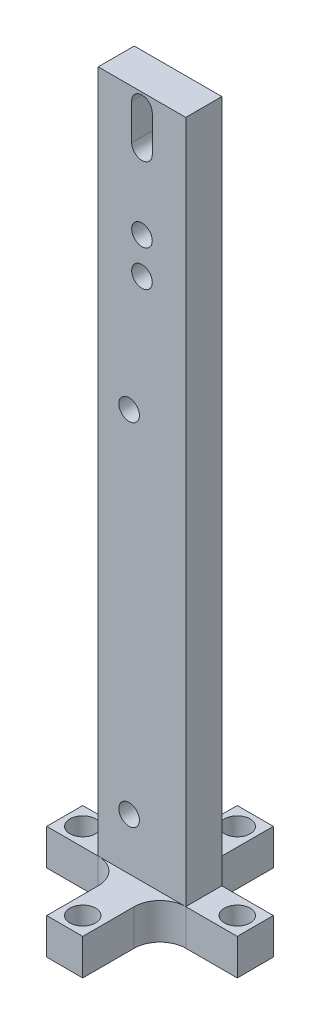
SolidWorks part; units mm, degrees
ref_plane "Front Plane" through (0, 0, 0) normal (0, 0, 1) x (1, 0, 0)
ref_plane "Top Plane" through (0, 0, 0) normal (0, 1, 0) x (1, 0, 0)
ref_plane "Right Plane" through (0, 0, 0) normal (1, 0, 0) x (0, 0, -1)
sketch "Sketch1" plane through (0, 0, 0) normal (0, 1, 0) x (1, 0, 0)
  line L1 (8.5, -3.5) -> (-8.5, -3.5)
  line L2 (8.5, -3.5) -> (8.5, 3.5)
  line L3 (8.5, 3.5) -> (-8.5, 3.5)
  line L4 (-8.5, -3.5) -> (-8.5, 3.5)
  line L5 (8.5, -3.5) -> (-8.5, 3.5) construction
  line L6 (8.5, 3.5) -> (-8.5, -3.5) construction
  point P0 (0, 0)
  dimension "D1" = 7
  dimension "D2" = 17
extrude "Boss-Extrude1" add sketch "Sketch1" along normal blind 139.7
sketch "Sketch2" plane through (0, 0, 0) normal (0, 1, 0) x (1, 0, 0)
  line L0 (-3.5, 3.5) -> (-3.5, 18.5)
  line L1 (-3.5, 18.5) -> (3.5, 18.5)
  line L2 (3.5, 18.5) -> (3.5, 3.5)
  line L3 (-3.5, 3.5) -> (-8.5, 3.5)
  line L4 (-8.5, 3.5) -> (-8.5, -3.5)
  line L5 (-8.5, -3.5) -> (8.5, -3.5)
  line L6 (8.5, -3.5) -> (8.5, 3.5)
  line L7 (8.5, 3.5) -> (-8.5, 3.5)
  line L9 (-8.5, -3.5) -> (-3.5, -3.5)
  line L11 (8.5, 3.5) -> (3.5, 3.5)
  line L12 (8.5, 3.5) -> (-8.5, 3.5) construction
  line L13 (-1000, 0) -> (49000, 0) construction
  line L14 (0, -1000) -> (0, 0) construction
  line L15 (3.5, -18.5) -> (3.5, -3.5)
  line L16 (-3.5, -18.5) -> (3.5, -18.5)
  line L17 (-3.5, -3.5) -> (-3.5, -18.5)
  line L18 (3.5, -3.5) -> (8.5, -3.5)
  line L19 (0, 3.5) -> (0, 49000) construction
  line L20 (8.5, 3.5) -> (18.5, 3.5)
  line L21 (18.5, 3.5) -> (18.5, -3.5)
  line L22 (18.5, -3.5) -> (8.5, -3.5)
  line L23 (8.5, 3.5) -> (8.5, -3.5) construction
  line L24 (-8.5, 3.5) -> (-18.5, 3.5)
  line L25 (-18.5, 3.5) -> (-18.5, -3.5)
  line L26 (-18.5, -3.5) -> (-8.5, -3.5)
  circle A0 centre (0, 15) radius 2.5
  circle A1 centre (15, 0) radius 2.5
  circle A2 centre (0, -15) radius 2.5
  circle A3 centre (-15, 0) radius 2.5
  point P8 (0, 18.5)
  point P37 (0, 0)
  dimension "D6" = 5
  dimension "D2" = 15
  dimension "D3" = 7
  dimension "D4" = 10
  dimension "D5" = 15
  dimension "D1" = 0
  dimension "D7" = 4
extrude "Boss-Extrude2" add sketch "Sketch2" along normal blind 7
fillet "Fillet1" radius 5 4 edges at (-3.5, 3.5, -3.5) (3.5, 3.5, -3.5) (3.5, 3.5, 3.5) (-3.5, 3.5, 3.5)
sketch "Sketch3" plane through (0, 0, 3.5) normal (0, 0, 1) x (1, 0, 0)
  line L0 (-2.5, 85.072) -> (-2.5, 17) construction
  line L1 (-8.5, 7) -> (8.5, 7) construction
  line L2 (-8.5, 139.7) -> (-8.5, 7) construction
  circle A0 centre (-2.5, 85.072) radius 2
  circle A1 centre (-2.5, 17) radius 2
  dimension "D1" = 4
  dimension "D2" = 68.072
  dimension "D3" = 10
  dimension "D4" = 6
extrude "Cut-Extrude1" cut sketch "Sketch3" against normal up to surface (7 mm away) up to face at (0, 73.35, -3.5)
sketch "Sketch4" plane through (0, 0, 3.5) normal (0, 0, 1) x (1, 0, 0)
  line L0 (0, 139.7) -> (0, 7) construction
  line L1 (-8.5, 139.7) -> (8.5, 139.7) construction
  line L2 (-3.5, 7) -> (3.5, 7) construction
  line L3 (0, 137.2) -> (0, 130.2) construction
  line L4 (2, 137.2) -> (2, 130.2)
  line L5 (-2, 137.2) -> (-2, 130.2)
  circle A0 centre (0, 115.7) radius 2
  circle A1 centre (0, 108.7) radius 2
  arc A2 (2, 137.2) -> (-2, 137.2) centre (0, 137.2) ccw
  arc A3 (-2, 130.2) -> (2, 130.2) centre (0, 130.2) ccw
  point P13 (0, 133.7)
  dimension "D1" = 4
  dimension "D4" = 2
  dimension "D2" = 7
  dimension "D3" = 24
  dimension "D5" = 7
  dimension "D6" = 2.5
extrude "Cut-Extrude2" cut sketch "Sketch4" against normal up to surface (7 mm away) up to face at (-0.5, 85.072, -3.5)
